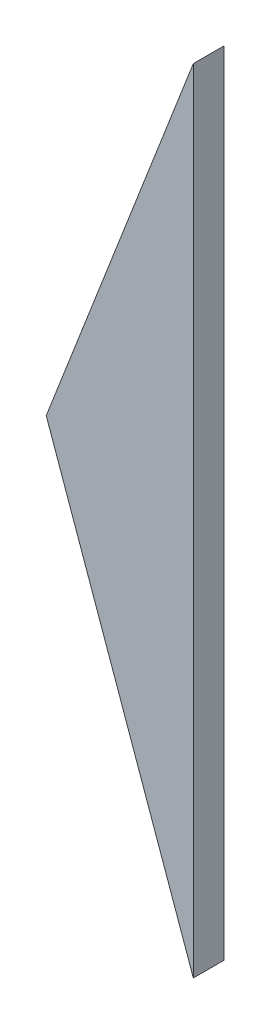
SolidWorks part; units mm, degrees
ref_plane "Plan de face" through (0, 0, 0) normal (0, 0, 1) x (1, 0, 0)
ref_plane "Plan de dessus" through (0, 0, 0) normal (0, 1, 0) x (1, 0, 0)
ref_plane "Plan de droite" through (0, 0, 0) normal (1, 0, 0) x (0, 0, -1)
sketch "Esquisse1" plane through (0, 0, 0) normal (0, 0, 1) x (1, 0, 0)
  line L0 (-25.7431, -66.2226) -> (-11.2502, -28.9405)
  line L1 (-11.2502, -28.9405) -> (-11.2502, -106.9523)
  line L2 (-11.2502, -106.9523) -> (-25.7431, -66.2226)
  line L3 (0, 0) -> (-26.1476, -67.2634) construction
  line L4 (2.5315, -145.6832) -> (-26.1174, -65.1707) construction
  dimension "D1" = 40
extrude "Boss.-Extru.1" add sketch "Esquisse1" against normal blind 3
